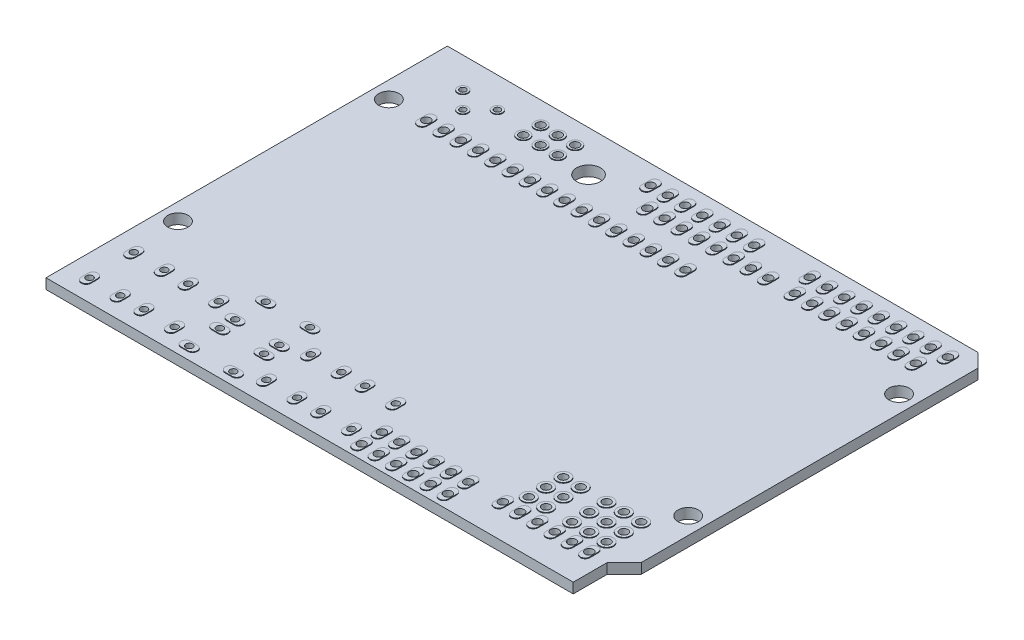
SolidWorks part; units mm, degrees
ref_plane "Front Plane" through (0, 0, 0) normal (0, 0, 1) x (1, 0, 0)
ref_plane "Top Plane" through (0, 0, 0) normal (0, 1, 0) x (1, 0, 0)
ref_plane "Right Plane" through (0, 0, 0) normal (1, 0, 0) x (0, 0, -1)
sketch "Sketch1" plane through (0, 0, 0) normal (0, 1, 0) x (1, 0, 0)
  line L0 (6.8, 54.47) -> (11.88, 54.47) construction
  line L1 (0, 0) -> (77.5, 0)
  line L2 (0, 0) -> (0, 59)
  line L3 (0, 59) -> (78, 59)
  line L4 (80, 7.5) -> (80, 57)
  line L5 (3.3, 9.6) -> (7.8, 9.6) construction
  line L6 (3.3, 9.6) -> (3.3, 3.1) construction
  line L7 (3.3, 3.1) -> (7.8, 3.1) construction
  line L8 (7.8, 9.6) -> (7.8, 3.1) construction
  line L9 (19.3, 6.25) -> (25.8, 6.25) construction
  line L10 (19.3, 6.25) -> (19.3, 1.75) construction
  line L11 (19.3, 1.75) -> (25.8, 1.75) construction
  line L12 (25.8, 6.25) -> (25.8, 1.75) construction
  line L13 (9.34, 54.47) -> (9.34, 51.93) construction
  line L14 (78, 59) -> (80, 57)
  line L15 (78, 59) -> (80, 59) construction
  line L16 (80, 59) -> (80, 57) construction
  line L17 (77.5, 0) -> (77.5, 5)
  line L18 (77.5, 5) -> (80, 7.5)
  line L19 (77.5, 0) -> (80, 0) construction
  line L20 (80, 0) -> (80, 7.5) construction
  line L21 (8, 47.9) -> (46.1, 47.9) construction
  circle A0 centre (17, 55.7) radius 0.6
  circle A1 centre (19.54, 55.7) radius 0.6
  circle A2 centre (22.08, 55.7) radius 0.6
  circle A3 centre (19.54, 53.16) radius 0.6
  circle A4 centre (22.08, 53.16) radius 0.6
  circle A5 centre (17, 53.16) radius 0.6
  circle A6 centre (32.7622, 56.1) radius 0.6
  circle A7 centre (35.4331, 52.95) radius 0.6
  circle A8 centre (35.3022, 56.1) radius 0.6
  circle A9 centre (37.8422, 56.1) radius 0.6
  circle A10 centre (40.3822, 56.1) radius 0.6
  circle A11 centre (42.9222, 56.1) radius 0.6
  circle A12 centre (45.4622, 56.1) radius 0.6
  circle A13 centre (48.0022, 56.1) radius 0.6
  circle A14 centre (37.9731, 52.95) radius 0.6
  circle A15 centre (40.5131, 52.95) radius 0.6
  circle A16 centre (43.0531, 52.95) radius 0.6
  circle A17 centre (45.5931, 52.95) radius 0.6
  circle A18 centre (48.1331, 52.95) radius 0.6
  circle A19 centre (50.6731, 52.95) radius 0.6
  circle A20 centre (53.2131, 52.95) radius 0.6
  circle A21 centre (56.1622, 56.1) radius 0.6
  circle A22 centre (57.1301, 52.95) radius 0.6
  circle A23 centre (59.6701, 52.95) radius 0.6
  circle A24 centre (62.2101, 52.95) radius 0.6
  circle A25 centre (64.7501, 52.95) radius 0.6
  circle A26 centre (67.2901, 52.95) radius 0.6
  circle A27 centre (69.8301, 52.95) radius 0.6
  circle A28 centre (72.3701, 52.95) radius 0.6
  circle A29 centre (74.9101, 52.95) radius 0.6
  circle A30 centre (58.7022, 56.1) radius 0.6
  circle A31 centre (61.2422, 56.1) radius 0.6
  circle A32 centre (63.7822, 56.1) radius 0.6
  circle A33 centre (66.3222, 56.1) radius 0.6
  circle A34 centre (68.8622, 56.1) radius 0.6
  circle A35 centre (71.4022, 56.1) radius 0.6
  circle A36 centre (73.9422, 56.1) radius 0.6
  circle A37 centre (76.4822, 56.1) radius 0.6
  circle A38 centre (8, 47.9) radius 0.6
  circle A39 centre (10.54, 47.9) radius 0.6
  circle A40 centre (13.08, 47.9) radius 0.6
  circle A41 centre (15.62, 47.9) radius 0.6
  circle A42 centre (18.16, 47.9) radius 0.6
  circle A43 centre (20.7, 47.9) radius 0.6
  circle A44 centre (23.24, 47.9) radius 0.6
  circle A45 centre (25.78, 47.9) radius 0.6
  circle A46 centre (28.32, 47.9) radius 0.6
  circle A47 centre (30.86, 47.9) radius 0.6
  circle A48 centre (33.4, 47.9) radius 0.6
  circle A49 centre (35.94, 47.9) radius 0.6
  circle A50 centre (38.48, 47.9) radius 0.6
  circle A51 centre (41.02, 47.9) radius 0.6
  circle A52 centre (43.56, 47.9) radius 0.6
  circle A53 centre (46.1, 47.9) radius 0.6
  circle A54 centre (74.9101, 4.95) radius 0.6
  circle A55 centre (72.3701, 4.95) radius 0.6
  circle A56 centre (69.8301, 4.95) radius 0.6
  circle A57 centre (67.2901, 4.95) radius 0.6
  circle A58 centre (64.7501, 4.95) radius 0.6
  circle A59 centre (62.2101, 4.95) radius 0.6
  circle A60 centre (59.6701, 4.95) radius 0.6 [skipped]
  circle A61 centre (57.1301, 4.95) radius 0.6
  circle A62 centre (54.5901, 4.95) radius 0.6
  circle A63 centre (52.0501, 4.95) radius 0.6
  circle A64 centre (49.5101, 4.95) radius 0.6
  circle A65 centre (46.9701, 4.95) radius 0.6
  circle A66 centre (44.4301, 4.95) radius 0.6
  circle A67 centre (57.1301, 1.95) radius 0.6
  circle A68 centre (54.5901, 1.95) radius 0.6
  circle A69 centre (52.0501, 1.95) radius 0.6
  circle A70 centre (49.5101, 1.95) radius 0.6
  circle A71 centre (46.9701, 1.95) radius 0.6
  circle A72 centre (44.4301, 1.95) radius 0.6
  circle A73 centre (63.4801, 7.49) radius 0.6
  circle A74 centre (74.9101, 7.49) radius 0.6
  circle A75 centre (72.3701, 7.49) radius 0.6
  circle A76 centre (69.8301, 7.49) radius 0.6
  circle A77 centre (74.9101, 10.03) radius 0.6
  circle A78 centre (72.3701, 10.03) radius 0.6
  circle A79 centre (69.8301, 10.03) radius 0.6
  circle A80 centre (74.9101, 12.57) radius 0.6
  circle A81 centre (72.3701, 12.57) radius 0.6
  circle A82 centre (69.8301, 12.57) radius 0.6
  circle A83 centre (66.0201, 7.49) radius 0.6
  circle A84 centre (66.0201, 10.03) radius 0.6
  circle A85 centre (66.0201, 12.57) radius 0.6
  circle A86 centre (63.4801, 10.03) radius 0.6
  circle A87 centre (63.4801, 12.57) radius 0.6
  circle A88 centre (2.5, 47.9) radius 1.5
  circle A89 centre (77.5, 47.9) radius 1.5
  circle A90 centre (77.5, 16.9) radius 1.5
  circle A91 centre (2.5, 16.9) radius 1.5
  circle A92 centre (3.3, 9.6) radius 0.5
  circle A93 centre (7.8, 9.6) radius 0.5
  circle A94 centre (7.8, 3.1) radius 0.5
  circle A95 centre (3.3, 3.1) radius 0.5
  circle A96 centre (11.3, 9.6) radius 0.5
  circle A97 centre (15.8, 9.6) radius 0.5
  circle A98 centre (15.8, 3.1) radius 0.5
  circle A99 centre (11.3, 3.1) radius 0.5
  circle A100 centre (29.3, 9.6) radius 0.5
  circle A101 centre (33.8, 9.6) radius 0.5
  circle A102 centre (33.8, 3.1) radius 0.5
  circle A103 centre (29.3, 3.1) radius 0.5
  circle A104 centre (41.8, 3.1) radius 0.5
  circle A105 centre (41.8, 9.6) radius 0.5
  circle A106 centre (37.3, 9.6) radius 0.5
  circle A107 centre (37.3, 3.1) radius 0.5
  circle A108 centre (19.3, 6.25) radius 0.5
  circle A109 centre (25.8, 6.25) radius 0.5
  circle A110 centre (25.8, 1.75) radius 0.5
  circle A111 centre (19.3, 1.75) radius 0.5
  circle A112 centre (19.3, 13) radius 0.5
  circle A113 centre (19.3, 8.5) radius 0.5
  circle A114 centre (25.8, 13) radius 0.5
  circle A115 centre (25.8, 8.5) radius 0.5
  circle A116 centre (6.8, 54.47) radius 0.45
  circle A117 centre (11.88, 54.47) radius 0.45
  circle A118 centre (9.34, 51.93) radius 0.45
  circle A119 centre (26.75, 53) radius 1.75
  point P1 (80, 59)
  point P3 (80, 0)
  point P243 (9.34, 54.47)
  dimension "D3" = 1.2
  dimension "D9" = 1.2
  dimension "D12" = 1.2
  dimension "D13" = 7
  dimension "D18" = 1.2
  dimension "D23" = 1.2
  dimension "D24" = 1.2
  dimension "D28" = 48
  dimension "D29" = 13
  dimension "D31" = 1.2
  dimension "D35" = 2
  dimension "D38" = 3
  dimension "D40" = 23.4
  dimension "D47" = 1
  dimension "D48" = 1
  dimension "D49" = 1
  dimension "D50" = 1
  dimension "D57" = 1
  dimension "D61" = 0.9
  dimension "D72" = 11.1
  dimension "D73" = 3.5
  dimension "D1" = 59
  dimension "D4" = 3.3
  dimension "D5" = 17
  dimension "D8" = 2.9
  dimension "D10" = 2
  dimension "D11" = 3.15
  dimension "D15" = 2.6709
  dimension "D16" = 2.9
  dimension "D17" = 3.15
  dimension "D19" = 3.917
  dimension "D21" = 15.7622
  dimension "D25" = 8
  dimension "D26" = 11.1
  dimension "D33" = 3.5
  dimension "D34" = 1.27
  dimension "D37" = 2.5
  dimension "D39" = 11.1
  dimension "D43" = 31
  dimension "D44" = 75
  dimension "D45" = 4.5
  dimension "D46" = 6.5
  dimension "D51" = 3.1
  dimension "D52" = 3.3
  dimension "D55" = 6.5
  dimension "D56" = 4.5
  dimension "D58" = 1.75
  dimension "D59" = 3.5
  dimension "D62" = 2.54
  dimension "D63" = 2.54
  dimension "D64" = 4.53
  dimension "D65" = 6.8
  dimension "D66" = 2
  dimension "D67" = 2
  dimension "D68" = 80
  dimension "D69" = 2.5
  dimension "D70" = 2.5
  dimension "D71" = 5
  dimension "D74" = 26.75
  dimension "D75" = 6
  dimension "D76" = 1.95
  dimension "D77" = 3
  dimension "D6" = 3
  dimension "D7" = 2
  dimension "D14" = 8
  dimension "D20" = 8
  dimension "D22" = 9
  dimension "D27" = 16
  dimension "D30" = 2
  dimension "D32" = 4
  dimension "D36" = 3
  dimension "D41" = 2
  dimension "D42" = 2
  dimension "D53" = 2
  dimension "D54" = 2
  dimension "D60" = 2
extrude "PCB" add sketch "Sketch1" against normal blind 1.5
sketch "Sketch2" plane through (0, 0, 0) normal (0, 1, 0) x (1, 0, 0)
  line L0 (32.7622, 56.7) -> (32.7622, 55.5) construction
  line L1 (32.7622, 56.7) -> (32.7622, 55.5) construction
  line L2 (33.4622, 56.7) -> (33.4622, 55.5)
  line L3 (32.0622, 56.7) -> (32.0622, 55.5)
  line L4 (35.3022, 56.7) -> (35.3022, 55.5) construction
  line L5 (35.3022, 56.7) -> (35.3022, 55.5) construction
  line L6 (36.0022, 56.7) -> (36.0022, 55.5)
  line L7 (34.6022, 56.7) -> (34.6022, 55.5)
  line L8 (37.8422, 56.7) -> (37.8422, 55.5) construction
  line L9 (37.8422, 56.7) -> (37.8422, 55.5) construction
  line L10 (38.5422, 56.7) -> (38.5422, 55.5)
  line L11 (37.1422, 56.7) -> (37.1422, 55.5)
  line L12 (40.3822, 56.7) -> (40.3822, 55.5) construction
  line L13 (40.3822, 56.7) -> (40.3822, 55.5) construction
  line L14 (41.0822, 56.7) -> (41.0822, 55.5)
  line L15 (39.6822, 56.7) -> (39.6822, 55.5)
  line L16 (42.9222, 56.7) -> (42.9222, 55.5) construction
  line L17 (42.9222, 56.7) -> (42.9222, 55.5) construction
  line L18 (43.6222, 56.7) -> (43.6222, 55.5)
  line L19 (42.2222, 56.7) -> (42.2222, 55.5)
  line L20 (45.4622, 56.7) -> (45.4622, 55.5) construction
  line L21 (45.4622, 56.7) -> (45.4622, 55.5) construction
  line L22 (46.1622, 56.7) -> (46.1622, 55.5)
  line L23 (44.7622, 56.7) -> (44.7622, 55.5)
  line L24 (48.0022, 56.7) -> (48.0022, 55.5) construction
  line L25 (48.0022, 56.7) -> (48.0022, 55.5) construction
  line L26 (48.7022, 56.7) -> (48.7022, 55.5)
  line L27 (47.3022, 56.7) -> (47.3022, 55.5)
  line L28 (35.4331, 53.55) -> (35.4331, 52.35) construction
  line L29 (36.1331, 53.55) -> (36.1331, 52.35)
  line L30 (34.7331, 53.55) -> (34.7331, 52.35)
  line L31 (56.1622, 56.7) -> (56.1622, 55.5) construction
  line L32 (56.8622, 56.7) -> (56.8622, 55.5)
  line L33 (55.4622, 56.7) -> (55.4622, 55.5)
  line L34 (57.1301, 53.55) -> (57.1301, 52.35) construction
  line L35 (57.8301, 53.55) -> (57.8301, 52.35)
  line L36 (56.4301, 53.55) -> (56.4301, 52.35)
  line L37 (8, 48.5) -> (8, 47.3) construction
  line L38 (8.7, 48.5) -> (8.7, 47.3)
  line L39 (7.3, 48.5) -> (7.3, 47.3)
  line L40 (3.3, 10.1) -> (3.3, 9.1) construction
  line L41 (4, 10.1) -> (4, 9.1)
  line L42 (2.6, 10.1) -> (2.6, 9.1)
  line L43 (18.8, 1.75) -> (19.8, 1.75) construction
  line L44 (18.8, 2.45) -> (19.8, 2.45)
  line L45 (18.8, 1.05) -> (19.8, 1.05)
  line L46 (29.3, 10.1) -> (29.3, 9.1) construction
  line L47 (30, 10.1) -> (30, 9.1)
  line L48 (28.6, 10.1) -> (28.6, 9.1)
  line L49 (44.4301, 5.55) -> (44.4301, 4.35) construction
  line L50 (45.1301, 5.55) -> (45.1301, 4.35)
  line L51 (43.7301, 5.55) -> (43.7301, 4.35)
  line L52 (62.2101, 4.35) -> (62.2101, 5.55) construction
  line L53 (61.5101, 4.35) -> (61.5101, 5.55)
  line L54 (62.9101, 4.35) -> (62.9101, 5.55)
  line L55 (7.8, 10.1) -> (7.8, 9.1) construction
  line L56 (8.5, 10.1) -> (8.5, 9.1)
  line L57 (7.1, 10.1) -> (7.1, 9.1)
  line L58 (7.8, 3.6) -> (7.8, 2.6) construction
  line L59 (8.5, 3.6) -> (8.5, 2.6)
  line L60 (7.1, 3.6) -> (7.1, 2.6)
  line L61 (37.9731, 53.55) -> (37.9731, 52.35) construction
  line L62 (38.6731, 53.55) -> (38.6731, 52.35)
  line L63 (37.2731, 53.55) -> (37.2731, 52.35)
  line L64 (59.6701, 53.55) -> (59.6701, 52.35) construction
  line L65 (60.3701, 53.55) -> (60.3701, 52.35)
  line L66 (58.9701, 53.55) -> (58.9701, 52.35)
  line L67 (40.5131, 53.55) -> (40.5131, 52.35) construction
  line L68 (41.2131, 53.55) -> (41.2131, 52.35)
  line L69 (39.8131, 53.55) -> (39.8131, 52.35)
  line L70 (62.2101, 53.55) -> (62.2101, 52.35) construction
  line L71 (62.9101, 53.55) -> (62.9101, 52.35)
  line L72 (61.5101, 53.55) -> (61.5101, 52.35)
  line L73 (43.0531, 53.55) -> (43.0531, 52.35) construction
  line L74 (43.7531, 53.55) -> (43.7531, 52.35)
  line L75 (42.3531, 53.55) -> (42.3531, 52.35)
  line L76 (64.7501, 53.55) -> (64.7501, 52.35) construction
  line L77 (65.4501, 53.55) -> (65.4501, 52.35)
  line L78 (64.0501, 53.55) -> (64.0501, 52.35)
  line L79 (45.5931, 53.55) -> (45.5931, 52.35) construction
  line L80 (46.2931, 53.55) -> (46.2931, 52.35)
  line L81 (44.8931, 53.55) -> (44.8931, 52.35)
  line L82 (67.2901, 53.55) -> (67.2901, 52.35) construction
  line L83 (67.9901, 53.55) -> (67.9901, 52.35)
  line L84 (66.5901, 53.55) -> (66.5901, 52.35)
  line L85 (48.1331, 53.55) -> (48.1331, 52.35) construction
  line L86 (48.8331, 53.55) -> (48.8331, 52.35)
  line L87 (47.4331, 53.55) -> (47.4331, 52.35)
  line L88 (69.8301, 53.55) -> (69.8301, 52.35) construction
  line L89 (70.5301, 53.55) -> (70.5301, 52.35)
  line L90 (69.1301, 53.55) -> (69.1301, 52.35)
  line L91 (50.6731, 53.55) -> (50.6731, 52.35) construction
  line L92 (51.3731, 53.55) -> (51.3731, 52.35)
  line L93 (49.9731, 53.55) -> (49.9731, 52.35)
  line L94 (72.3701, 53.55) -> (72.3701, 52.35) construction
  line L95 (73.0701, 53.55) -> (73.0701, 52.35)
  line L96 (71.6701, 53.55) -> (71.6701, 52.35)
  line L97 (53.2131, 53.55) -> (53.2131, 52.35) construction
  line L98 (53.9131, 53.55) -> (53.9131, 52.35)
  line L99 (52.5131, 53.55) -> (52.5131, 52.35)
  line L100 (74.9101, 53.55) -> (74.9101, 52.35) construction
  line L101 (75.6101, 53.55) -> (75.6101, 52.35)
  line L102 (74.2101, 53.55) -> (74.2101, 52.35)
  line L103 (58.7022, 56.7) -> (58.7022, 55.5) construction
  line L104 (59.4022, 56.7) -> (59.4022, 55.5)
  line L105 (58.0022, 56.7) -> (58.0022, 55.5)
  line L106 (61.2422, 56.7) -> (61.2422, 55.5) construction
  line L107 (61.9422, 56.7) -> (61.9422, 55.5)
  line L108 (60.5422, 56.7) -> (60.5422, 55.5)
  line L109 (63.7822, 56.7) -> (63.7822, 55.5) construction
  line L110 (64.4822, 56.7) -> (64.4822, 55.5)
  line L111 (63.0822, 56.7) -> (63.0822, 55.5)
  line L112 (66.3222, 56.7) -> (66.3222, 55.5) construction
  line L113 (67.0222, 56.7) -> (67.0222, 55.5)
  line L114 (65.6222, 56.7) -> (65.6222, 55.5)
  line L115 (68.8622, 56.7) -> (68.8622, 55.5) construction
  line L116 (69.5622, 56.7) -> (69.5622, 55.5)
  line L117 (68.1622, 56.7) -> (68.1622, 55.5)
  line L118 (71.4022, 56.7) -> (71.4022, 55.5) construction
  line L119 (72.1022, 56.7) -> (72.1022, 55.5)
  line L120 (70.7022, 56.7) -> (70.7022, 55.5)
  line L121 (73.9422, 56.7) -> (73.9422, 55.5) construction
  line L122 (74.6422, 56.7) -> (74.6422, 55.5)
  line L123 (73.2422, 56.7) -> (73.2422, 55.5)
  line L124 (76.4822, 56.7) -> (76.4822, 55.5) construction
  line L125 (77.1822, 56.7) -> (77.1822, 55.5)
  line L126 (75.7822, 56.7) -> (75.7822, 55.5)
  line L127 (10.54, 48.5) -> (10.54, 47.3) construction
  line L128 (11.24, 48.5) -> (11.24, 47.3)
  line L129 (9.84, 48.5) -> (9.84, 47.3)
  line L130 (13.08, 48.5) -> (13.08, 47.3) construction
  line L131 (13.78, 48.5) -> (13.78, 47.3)
  line L132 (12.38, 48.5) -> (12.38, 47.3)
  line L133 (15.62, 48.5) -> (15.62, 47.3) construction
  line L134 (16.32, 48.5) -> (16.32, 47.3)
  line L135 (14.92, 48.5) -> (14.92, 47.3)
  line L136 (18.16, 48.5) -> (18.16, 47.3) construction
  line L137 (18.86, 48.5) -> (18.86, 47.3)
  line L138 (17.46, 48.5) -> (17.46, 47.3)
  line L139 (20.7, 48.5) -> (20.7, 47.3) construction
  line L140 (21.4, 48.5) -> (21.4, 47.3)
  line L141 (20, 48.5) -> (20, 47.3)
  line L142 (23.24, 48.5) -> (23.24, 47.3) construction
  line L143 (23.94, 48.5) -> (23.94, 47.3)
  line L144 (22.54, 48.5) -> (22.54, 47.3)
  line L145 (25.78, 48.5) -> (25.78, 47.3) construction
  line L146 (26.48, 48.5) -> (26.48, 47.3)
  line L147 (25.08, 48.5) -> (25.08, 47.3)
  line L148 (28.32, 48.5) -> (28.32, 47.3) construction
  line L149 (29.02, 48.5) -> (29.02, 47.3)
  line L150 (27.62, 48.5) -> (27.62, 47.3)
  line L151 (30.86, 48.5) -> (30.86, 47.3) construction
  line L152 (31.56, 48.5) -> (31.56, 47.3)
  line L153 (30.16, 48.5) -> (30.16, 47.3)
  line L154 (33.4, 48.5) -> (33.4, 47.3) construction
  line L155 (34.1, 48.5) -> (34.1, 47.3)
  line L156 (32.7, 48.5) -> (32.7, 47.3)
  line L157 (35.94, 48.5) -> (35.94, 47.3) construction
  line L158 (36.64, 48.5) -> (36.64, 47.3)
  line L159 (35.24, 48.5) -> (35.24, 47.3)
  line L160 (38.48, 48.5) -> (38.48, 47.3) construction
  line L161 (39.18, 48.5) -> (39.18, 47.3)
  line L162 (37.78, 48.5) -> (37.78, 47.3)
  line L163 (41.02, 48.5) -> (41.02, 47.3) construction
  line L164 (41.72, 48.5) -> (41.72, 47.3)
  line L165 (40.32, 48.5) -> (40.32, 47.3)
  line L166 (43.56, 48.5) -> (43.56, 47.3) construction
  line L167 (44.26, 48.5) -> (44.26, 47.3)
  line L168 (42.86, 48.5) -> (42.86, 47.3)
  line L169 (46.1, 48.5) -> (46.1, 47.3) construction
  line L170 (46.8, 48.5) -> (46.8, 47.3)
  line L171 (45.4, 48.5) -> (45.4, 47.3)
  line L172 (46.9701, 5.55) -> (46.9701, 4.35) construction
  line L173 (47.6701, 5.55) -> (47.6701, 4.35)
  line L174 (46.2701, 5.55) -> (46.2701, 4.35)
  line L175 (49.5101, 5.55) -> (49.5101, 4.35) construction
  line L176 (50.2101, 5.55) -> (50.2101, 4.35)
  line L177 (48.8101, 5.55) -> (48.8101, 4.35)
  line L178 (52.0501, 5.55) -> (52.0501, 4.35) construction
  line L179 (52.7501, 5.55) -> (52.7501, 4.35)
  line L180 (51.3501, 5.55) -> (51.3501, 4.35)
  line L181 (54.5901, 5.55) -> (54.5901, 4.35) construction
  line L182 (55.2901, 5.55) -> (55.2901, 4.35)
  line L183 (53.8901, 5.55) -> (53.8901, 4.35)
  line L184 (57.1301, 5.55) -> (57.1301, 4.35) construction
  line L185 (57.8301, 5.55) -> (57.8301, 4.35)
  line L186 (56.4301, 5.55) -> (56.4301, 4.35)
  line L187 (46.9701, 2.55) -> (46.9701, 1.35) construction
  line L188 (47.6701, 2.55) -> (47.6701, 1.35)
  line L189 (46.2701, 2.55) -> (46.2701, 1.35)
  line L190 (49.5101, 2.55) -> (49.5101, 1.35) construction
  line L191 (50.2101, 2.55) -> (50.2101, 1.35)
  line L192 (48.8101, 2.55) -> (48.8101, 1.35)
  line L193 (52.0501, 2.55) -> (52.0501, 1.35) construction
  line L194 (52.7501, 2.55) -> (52.7501, 1.35)
  line L195 (51.3501, 2.55) -> (51.3501, 1.35)
  line L196 (54.5901, 2.55) -> (54.5901, 1.35) construction
  line L197 (55.2901, 2.55) -> (55.2901, 1.35)
  line L198 (53.8901, 2.55) -> (53.8901, 1.35)
  line L199 (57.1301, 2.55) -> (57.1301, 1.35) construction
  line L200 (57.8301, 2.55) -> (57.8301, 1.35)
  line L201 (56.4301, 2.55) -> (56.4301, 1.35)
  line L202 (44.4301, 2.55) -> (44.4301, 1.35) construction
  line L203 (45.1301, 2.55) -> (45.1301, 1.35)
  line L204 (43.7301, 2.55) -> (43.7301, 1.35)
  line L205 (64.7501, 4.35) -> (64.7501, 5.55) construction
  line L206 (64.0501, 4.35) -> (64.0501, 5.55)
  line L207 (65.4501, 4.35) -> (65.4501, 5.55)
  line L208 (67.2901, 4.35) -> (67.2901, 5.55) construction
  line L209 (66.5901, 4.35) -> (66.5901, 5.55)
  line L210 (67.9901, 4.35) -> (67.9901, 5.55)
  line L211 (69.8301, 4.35) -> (69.8301, 5.55) construction
  line L212 (69.1301, 4.35) -> (69.1301, 5.55)
  line L213 (70.5301, 4.35) -> (70.5301, 5.55)
  line L214 (72.3701, 4.35) -> (72.3701, 5.55) construction
  line L215 (71.6701, 4.35) -> (71.6701, 5.55)
  line L216 (73.0701, 4.35) -> (73.0701, 5.55)
  line L217 (74.9101, 4.35) -> (74.9101, 5.55) construction
  line L218 (74.2101, 4.35) -> (74.2101, 5.55)
  line L219 (75.6101, 4.35) -> (75.6101, 5.55)
  line L220 (3.3, 3.6) -> (3.3, 2.6) construction
  line L221 (4, 3.6) -> (4, 2.6)
  line L222 (2.6, 3.6) -> (2.6, 2.6)
  line L223 (11.3, 10.1) -> (11.3, 9.1) construction
  line L224 (12, 10.1) -> (12, 9.1)
  line L225 (10.6, 10.1) -> (10.6, 9.1)
  line L226 (15.8, 10.1) -> (15.8, 9.1) construction
  line L227 (16.5, 10.1) -> (16.5, 9.1)
  line L228 (15.1, 10.1) -> (15.1, 9.1)
  line L229 (15.8, 3.6) -> (15.8, 2.6) construction
  line L230 (16.5, 3.6) -> (16.5, 2.6)
  line L231 (15.1, 3.6) -> (15.1, 2.6)
  line L232 (11.3, 3.6) -> (11.3, 2.6) construction
  line L233 (12, 3.6) -> (12, 2.6)
  line L234 (10.6, 3.6) -> (10.6, 2.6)
  line L235 (25.3, 1.75) -> (26.3, 1.75) construction
  line L236 (25.3, 2.45) -> (26.3, 2.45)
  line L237 (25.3, 1.05) -> (26.3, 1.05)
  line L238 (25.3, 6.25) -> (26.3, 6.25) construction
  line L239 (25.3, 6.95) -> (26.3, 6.95)
  line L240 (25.3, 5.55) -> (26.3, 5.55)
  line L241 (18.8, 6.25) -> (19.8, 6.25) construction
  line L242 (18.8, 6.95) -> (19.8, 6.95)
  line L243 (18.8, 5.55) -> (19.8, 5.55)
  line L244 (18.8, 8.5) -> (19.8, 8.5) construction
  line L245 (18.8, 9.2) -> (19.8, 9.2)
  line L246 (18.8, 7.8) -> (19.8, 7.8)
  line L247 (25.3, 8.5) -> (26.3, 8.5) construction
  line L248 (25.3, 9.2) -> (26.3, 9.2)
  line L249 (25.3, 7.8) -> (26.3, 7.8)
  line L250 (25.3, 13) -> (26.3, 13) construction
  line L251 (25.3, 13.7) -> (26.3, 13.7)
  line L252 (25.3, 12.3) -> (26.3, 12.3)
  line L253 (18.8, 13) -> (19.8, 13) construction
  line L254 (18.8, 13.7) -> (19.8, 13.7)
  line L255 (18.8, 12.3) -> (19.8, 12.3)
  line L256 (33.8, 10.1) -> (33.8, 9.1) construction
  line L257 (34.5, 10.1) -> (34.5, 9.1)
  line L258 (33.1, 10.1) -> (33.1, 9.1)
  line L259 (33.8, 3.6) -> (33.8, 2.6) construction
  line L260 (34.5, 3.6) -> (34.5, 2.6)
  line L261 (33.1, 3.6) -> (33.1, 2.6)
  line L262 (29.3, 3.6) -> (29.3, 2.6) construction
  line L263 (30, 3.6) -> (30, 2.6)
  line L264 (28.6, 3.6) -> (28.6, 2.6)
  line L265 (37.3, 10.1) -> (37.3, 9.1) construction
  line L266 (38, 10.1) -> (38, 9.1)
  line L267 (36.6, 10.1) -> (36.6, 9.1)
  line L268 (41.8, 10.1) -> (41.8, 9.1) construction
  line L269 (42.5, 10.1) -> (42.5, 9.1)
  line L270 (41.1, 10.1) -> (41.1, 9.1)
  line L271 (41.8, 3.6) -> (41.8, 2.6) construction
  line L272 (42.5, 3.6) -> (42.5, 2.6)
  line L273 (41.1, 3.6) -> (41.1, 2.6)
  line L274 (37.3, 3.6) -> (37.3, 2.6) construction
  line L275 (38, 3.6) -> (38, 2.6)
  line L276 (36.6, 3.6) -> (36.6, 2.6)
  circle A0 centre (17, 55.7) radius 0.6 construction
  circle A1 centre (17, 53.16) radius 0.6 construction
  circle A2 centre (19.54, 53.16) radius 0.6 construction
  circle A3 centre (19.54, 55.7) radius 0.6 construction
  circle A4 centre (22.08, 55.7) radius 0.6 construction
  circle A5 centre (22.08, 53.16) radius 0.6 construction
  circle A6 centre (17, 55.7) radius 0.6
  circle A7 centre (17, 53.16) radius 0.6
  circle A8 centre (19.54, 53.16) radius 0.6
  circle A9 centre (19.54, 55.7) radius 0.6
  circle A10 centre (22.08, 55.7) radius 0.6
  circle A11 centre (22.08, 53.16) radius 0.6
  circle A12 centre (17, 55.7) radius 0.9
  circle A13 centre (17, 53.16) radius 0.9
  circle A14 centre (19.54, 53.16) radius 0.9
  circle A15 centre (19.54, 55.7) radius 0.9
  circle A16 centre (22.08, 55.7) radius 0.9
  circle A17 centre (22.08, 53.16) radius 0.9
  circle A18 centre (32.7622, 56.1) radius 0.6 construction
  circle A19 centre (32.7622, 56.1) radius 0.6
  arc A20 (33.4622, 56.7) -> (32.0622, 56.7) centre (32.7622, 56.7) ccw
  arc A21 (32.0622, 55.5) -> (33.4622, 55.5) centre (32.7622, 55.5) ccw
  circle A22 centre (35.3022, 56.1) radius 0.6
  arc A23 (36.0022, 56.7) -> (34.6022, 56.7) centre (35.3022, 56.7) ccw
  arc A24 (34.6022, 55.5) -> (36.0022, 55.5) centre (35.3022, 55.5) ccw
  circle A25 centre (37.8422, 56.1) radius 0.6
  arc A26 (38.5422, 56.7) -> (37.1422, 56.7) centre (37.8422, 56.7) ccw
  arc A27 (37.1422, 55.5) -> (38.5422, 55.5) centre (37.8422, 55.5) ccw
  circle A28 centre (40.3822, 56.1) radius 0.6
  arc A29 (41.0822, 56.7) -> (39.6822, 56.7) centre (40.3822, 56.7) ccw
  arc A30 (39.6822, 55.5) -> (41.0822, 55.5) centre (40.3822, 55.5) ccw
  circle A31 centre (42.9222, 56.1) radius 0.6
  arc A32 (43.6222, 56.7) -> (42.2222, 56.7) centre (42.9222, 56.7) ccw
  arc A33 (42.2222, 55.5) -> (43.6222, 55.5) centre (42.9222, 55.5) ccw
  circle A34 centre (45.4622, 56.1) radius 0.6
  arc A35 (46.1622, 56.7) -> (44.7622, 56.7) centre (45.4622, 56.7) ccw
  arc A36 (44.7622, 55.5) -> (46.1622, 55.5) centre (45.4622, 55.5) ccw
  circle A37 centre (48.0022, 56.1) radius 0.6
  arc A38 (48.7022, 56.7) -> (47.3022, 56.7) centre (48.0022, 56.7) ccw
  arc A39 (47.3022, 55.5) -> (48.7022, 55.5) centre (48.0022, 55.5) ccw
  circle A40 centre (35.4331, 52.95) radius 0.6 construction
  circle A41 centre (56.1622, 56.1) radius 0.6 construction
  circle A42 centre (57.1301, 52.95) radius 0.6 construction
  circle A43 centre (8, 47.9) radius 0.6 construction
  circle A44 centre (35.4331, 52.95) radius 0.6
  circle A45 centre (56.1622, 56.1) radius 0.6
  circle A46 centre (57.1301, 52.95) radius 0.6
  circle A47 centre (8, 47.9) radius 0.6
  arc A48 (36.1331, 53.55) -> (34.7331, 53.55) centre (35.4331, 53.55) ccw
  arc A49 (34.7331, 52.35) -> (36.1331, 52.35) centre (35.4331, 52.35) ccw
  arc A50 (56.8622, 56.7) -> (55.4622, 56.7) centre (56.1622, 56.7) ccw
  arc A51 (55.4622, 55.5) -> (56.8622, 55.5) centre (56.1622, 55.5) ccw
  arc A52 (57.8301, 53.55) -> (56.4301, 53.55) centre (57.1301, 53.55) ccw
  arc A53 (56.4301, 52.35) -> (57.8301, 52.35) centre (57.1301, 52.35) ccw
  arc A54 (8.7, 48.5) -> (7.3, 48.5) centre (8, 48.5) ccw
  arc A55 (7.3, 47.3) -> (8.7, 47.3) centre (8, 47.3) ccw
  circle A56 centre (37.9731, 52.95) radius 0.6
  circle A57 centre (19.3, 1.75) radius 0.5 construction
  circle A58 centre (29.3, 9.6) radius 0.5 construction
  circle A59 centre (44.4301, 4.95) radius 0.6 construction
  circle A60 centre (62.2101, 4.95) radius 0.6 construction
  circle A61 centre (63.4801, 7.49) radius 0.6 construction
  circle A62 centre (69.8301, 7.49) radius 0.6 construction
  circle A63 centre (3.3, 9.6) radius 0.5 construction
  circle A64 centre (19.3, 1.75) radius 0.5
  circle A65 centre (29.3, 9.6) radius 0.5
  circle A66 centre (44.4301, 4.95) radius 0.6
  circle A67 centre (62.2101, 4.95) radius 0.6
  circle A68 centre (63.4801, 7.49) radius 0.6
  circle A69 centre (69.8301, 7.49) radius 0.6
  circle A70 centre (3.3, 9.6) radius 0.5
  arc A71 (4, 10.1) -> (2.6, 10.1) centre (3.3, 10.1) ccw
  arc A72 (18.8, 2.45) -> (18.8, 1.05) centre (18.8, 1.75) ccw
  arc A73 (19.8, 1.05) -> (19.8, 2.45) centre (19.8, 1.75) ccw
  arc A74 (30, 10.1) -> (28.6, 10.1) centre (29.3, 10.1) ccw
  arc A75 (28.6, 9.1) -> (30, 9.1) centre (29.3, 9.1) ccw
  arc A76 (45.1301, 5.55) -> (43.7301, 5.55) centre (44.4301, 5.55) ccw
  arc A77 (43.7301, 4.35) -> (45.1301, 4.35) centre (44.4301, 4.35) ccw
  arc A78 (61.5101, 4.35) -> (62.9101, 4.35) centre (62.2101, 4.35) ccw
  arc A79 (62.9101, 5.55) -> (61.5101, 5.55) centre (62.2101, 5.55) ccw
  circle A80 centre (63.4801, 12.57) radius 0.6 construction
  circle A81 centre (63.4801, 10.03) radius 0.6 construction
  circle A82 centre (66.0201, 7.49) radius 0.6 construction
  circle A83 centre (66.0201, 10.03) radius 0.6 construction
  arc A84 (2.6, 9.1) -> (4, 9.1) centre (3.3, 9.1) ccw
  circle A85 centre (59.6701, 52.95) radius 0.6
  arc A86 (38.6731, 53.55) -> (37.2731, 53.55) centre (37.9731, 53.55) ccw
  arc A87 (37.2731, 52.35) -> (38.6731, 52.35) centre (37.9731, 52.35) ccw
  arc A88 (60.3701, 53.55) -> (58.9701, 53.55) centre (59.6701, 53.55) ccw
  arc A89 (58.9701, 52.35) -> (60.3701, 52.35) centre (59.6701, 52.35) ccw
  circle A90 centre (40.5131, 52.95) radius 0.6
  circle A91 centre (62.2101, 52.95) radius 0.6
  arc A92 (41.2131, 53.55) -> (39.8131, 53.55) centre (40.5131, 53.55) ccw
  arc A93 (39.8131, 52.35) -> (41.2131, 52.35) centre (40.5131, 52.35) ccw
  arc A94 (62.9101, 53.55) -> (61.5101, 53.55) centre (62.2101, 53.55) ccw
  arc A95 (61.5101, 52.35) -> (62.9101, 52.35) centre (62.2101, 52.35) ccw
  circle A96 centre (43.0531, 52.95) radius 0.6
  circle A97 centre (64.7501, 52.95) radius 0.6
  arc A98 (43.7531, 53.55) -> (42.3531, 53.55) centre (43.0531, 53.55) ccw
  arc A99 (42.3531, 52.35) -> (43.7531, 52.35) centre (43.0531, 52.35) ccw
  arc A100 (65.4501, 53.55) -> (64.0501, 53.55) centre (64.7501, 53.55) ccw
  arc A101 (64.0501, 52.35) -> (65.4501, 52.35) centre (64.7501, 52.35) ccw
  circle A102 centre (45.5931, 52.95) radius 0.6
  circle A103 centre (67.2901, 52.95) radius 0.6
  arc A104 (46.2931, 53.55) -> (44.8931, 53.55) centre (45.5931, 53.55) ccw
  arc A105 (44.8931, 52.35) -> (46.2931, 52.35) centre (45.5931, 52.35) ccw
  arc A106 (67.9901, 53.55) -> (66.5901, 53.55) centre (67.2901, 53.55) ccw
  arc A107 (66.5901, 52.35) -> (67.9901, 52.35) centre (67.2901, 52.35) ccw
  circle A108 centre (48.1331, 52.95) radius 0.6
  circle A109 centre (69.8301, 52.95) radius 0.6
  arc A110 (48.8331, 53.55) -> (47.4331, 53.55) centre (48.1331, 53.55) ccw
  arc A111 (47.4331, 52.35) -> (48.8331, 52.35) centre (48.1331, 52.35) ccw
  arc A112 (70.5301, 53.55) -> (69.1301, 53.55) centre (69.8301, 53.55) ccw
  arc A113 (69.1301, 52.35) -> (70.5301, 52.35) centre (69.8301, 52.35) ccw
  circle A114 centre (50.6731, 52.95) radius 0.6
  circle A115 centre (72.3701, 52.95) radius 0.6
  arc A116 (51.3731, 53.55) -> (49.9731, 53.55) centre (50.6731, 53.55) ccw
  arc A117 (49.9731, 52.35) -> (51.3731, 52.35) centre (50.6731, 52.35) ccw
  arc A118 (73.0701, 53.55) -> (71.6701, 53.55) centre (72.3701, 53.55) ccw
  arc A119 (71.6701, 52.35) -> (73.0701, 52.35) centre (72.3701, 52.35) ccw
  circle A120 centre (53.2131, 52.95) radius 0.6
  circle A121 centre (74.9101, 52.95) radius 0.6
  arc A122 (53.9131, 53.55) -> (52.5131, 53.55) centre (53.2131, 53.55) ccw
  arc A123 (52.5131, 52.35) -> (53.9131, 52.35) centre (53.2131, 52.35) ccw
  arc A124 (75.6101, 53.55) -> (74.2101, 53.55) centre (74.9101, 53.55) ccw
  arc A125 (74.2101, 52.35) -> (75.6101, 52.35) centre (74.9101, 52.35) ccw
  circle A126 centre (58.7022, 56.1) radius 0.6
  arc A127 (59.4022, 56.7) -> (58.0022, 56.7) centre (58.7022, 56.7) ccw
  arc A128 (58.0022, 55.5) -> (59.4022, 55.5) centre (58.7022, 55.5) ccw
  circle A129 centre (61.2422, 56.1) radius 0.6
  arc A130 (61.9422, 56.7) -> (60.5422, 56.7) centre (61.2422, 56.7) ccw
  arc A131 (60.5422, 55.5) -> (61.9422, 55.5) centre (61.2422, 55.5) ccw
  circle A132 centre (63.7822, 56.1) radius 0.6
  arc A133 (64.4822, 56.7) -> (63.0822, 56.7) centre (63.7822, 56.7) ccw
  arc A134 (63.0822, 55.5) -> (64.4822, 55.5) centre (63.7822, 55.5) ccw
  circle A135 centre (66.3222, 56.1) radius 0.6
  arc A136 (67.0222, 56.7) -> (65.6222, 56.7) centre (66.3222, 56.7) ccw
  arc A137 (65.6222, 55.5) -> (67.0222, 55.5) centre (66.3222, 55.5) ccw
  circle A138 centre (68.8622, 56.1) radius 0.6
  arc A139 (69.5622, 56.7) -> (68.1622, 56.7) centre (68.8622, 56.7) ccw
  arc A140 (68.1622, 55.5) -> (69.5622, 55.5) centre (68.8622, 55.5) ccw
  circle A141 centre (71.4022, 56.1) radius 0.6
  arc A142 (72.1022, 56.7) -> (70.7022, 56.7) centre (71.4022, 56.7) ccw
  arc A143 (70.7022, 55.5) -> (72.1022, 55.5) centre (71.4022, 55.5) ccw
  circle A144 centre (73.9422, 56.1) radius 0.6
  arc A145 (74.6422, 56.7) -> (73.2422, 56.7) centre (73.9422, 56.7) ccw
  arc A146 (73.2422, 55.5) -> (74.6422, 55.5) centre (73.9422, 55.5) ccw
  circle A147 centre (76.4822, 56.1) radius 0.6
  arc A148 (77.1822, 56.7) -> (75.7822, 56.7) centre (76.4822, 56.7) ccw
  arc A149 (75.7822, 55.5) -> (77.1822, 55.5) centre (76.4822, 55.5) ccw
  circle A150 centre (10.54, 47.9) radius 0.6
  arc A151 (11.24, 48.5) -> (9.84, 48.5) centre (10.54, 48.5) ccw
  arc A152 (9.84, 47.3) -> (11.24, 47.3) centre (10.54, 47.3) ccw
  circle A153 centre (13.08, 47.9) radius 0.6
  arc A154 (13.78, 48.5) -> (12.38, 48.5) centre (13.08, 48.5) ccw
  arc A155 (12.38, 47.3) -> (13.78, 47.3) centre (13.08, 47.3) ccw
  circle A156 centre (15.62, 47.9) radius 0.6
  arc A157 (16.32, 48.5) -> (14.92, 48.5) centre (15.62, 48.5) ccw
  arc A158 (14.92, 47.3) -> (16.32, 47.3) centre (15.62, 47.3) ccw
  circle A159 centre (18.16, 47.9) radius 0.6
  arc A160 (18.86, 48.5) -> (17.46, 48.5) centre (18.16, 48.5) ccw
  arc A161 (17.46, 47.3) -> (18.86, 47.3) centre (18.16, 47.3) ccw
  circle A162 centre (20.7, 47.9) radius 0.6
  arc A163 (21.4, 48.5) -> (20, 48.5) centre (20.7, 48.5) ccw
  arc A164 (20, 47.3) -> (21.4, 47.3) centre (20.7, 47.3) ccw
  circle A165 centre (23.24, 47.9) radius 0.6
  arc A166 (23.94, 48.5) -> (22.54, 48.5) centre (23.24, 48.5) ccw
  arc A167 (22.54, 47.3) -> (23.94, 47.3) centre (23.24, 47.3) ccw
  circle A168 centre (25.78, 47.9) radius 0.6
  arc A169 (26.48, 48.5) -> (25.08, 48.5) centre (25.78, 48.5) ccw
  arc A170 (25.08, 47.3) -> (26.48, 47.3) centre (25.78, 47.3) ccw
  circle A171 centre (28.32, 47.9) radius 0.6
  arc A172 (29.02, 48.5) -> (27.62, 48.5) centre (28.32, 48.5) ccw
  arc A173 (27.62, 47.3) -> (29.02, 47.3) centre (28.32, 47.3) ccw
  circle A174 centre (30.86, 47.9) radius 0.6
  arc A175 (31.56, 48.5) -> (30.16, 48.5) centre (30.86, 48.5) ccw
  arc A176 (30.16, 47.3) -> (31.56, 47.3) centre (30.86, 47.3) ccw
  circle A177 centre (33.4, 47.9) radius 0.6
  arc A178 (34.1, 48.5) -> (32.7, 48.5) centre (33.4, 48.5) ccw
  arc A179 (32.7, 47.3) -> (34.1, 47.3) centre (33.4, 47.3) ccw
  circle A180 centre (35.94, 47.9) radius 0.6
  arc A181 (36.64, 48.5) -> (35.24, 48.5) centre (35.94, 48.5) ccw
  arc A182 (35.24, 47.3) -> (36.64, 47.3) centre (35.94, 47.3) ccw
  circle A183 centre (38.48, 47.9) radius 0.6
  arc A184 (39.18, 48.5) -> (37.78, 48.5) centre (38.48, 48.5) ccw
  arc A185 (37.78, 47.3) -> (39.18, 47.3) centre (38.48, 47.3) ccw
  circle A186 centre (41.02, 47.9) radius 0.6
  arc A187 (41.72, 48.5) -> (40.32, 48.5) centre (41.02, 48.5) ccw
  arc A188 (40.32, 47.3) -> (41.72, 47.3) centre (41.02, 47.3) ccw
  circle A189 centre (43.56, 47.9) radius 0.6
  arc A190 (44.26, 48.5) -> (42.86, 48.5) centre (43.56, 48.5) ccw
  arc A191 (42.86, 47.3) -> (44.26, 47.3) centre (43.56, 47.3) ccw
  circle A192 centre (46.1, 47.9) radius 0.6
  arc A193 (46.8, 48.5) -> (45.4, 48.5) centre (46.1, 48.5) ccw
  arc A194 (45.4, 47.3) -> (46.8, 47.3) centre (46.1, 47.3) ccw
  circle A195 centre (46.9701, 4.95) radius 0.6
  arc A196 (47.6701, 5.55) -> (46.2701, 5.55) centre (46.9701, 5.55) ccw
  arc A197 (46.2701, 4.35) -> (47.6701, 4.35) centre (46.9701, 4.35) ccw
  circle A198 centre (49.5101, 4.95) radius 0.6
  arc A199 (50.2101, 5.55) -> (48.8101, 5.55) centre (49.5101, 5.55) ccw
  arc A200 (48.8101, 4.35) -> (50.2101, 4.35) centre (49.5101, 4.35) ccw
  circle A201 centre (52.0501, 4.95) radius 0.6
  arc A202 (52.7501, 5.55) -> (51.3501, 5.55) centre (52.0501, 5.55) ccw
  arc A203 (51.3501, 4.35) -> (52.7501, 4.35) centre (52.0501, 4.35) ccw
  circle A204 centre (54.5901, 4.95) radius 0.6
  arc A205 (55.2901, 5.55) -> (53.8901, 5.55) centre (54.5901, 5.55) ccw
  arc A206 (53.8901, 4.35) -> (55.2901, 4.35) centre (54.5901, 4.35) ccw
  circle A207 centre (57.1301, 4.95) radius 0.6
  arc A208 (57.8301, 5.55) -> (56.4301, 5.55) centre (57.1301, 5.55) ccw
  arc A209 (56.4301, 4.35) -> (57.8301, 4.35) centre (57.1301, 4.35) ccw
  circle A210 centre (46.9701, 1.95) radius 0.6
  arc A211 (47.6701, 2.55) -> (46.2701, 2.55) centre (46.9701, 2.55) ccw
  arc A212 (46.2701, 1.35) -> (47.6701, 1.35) centre (46.9701, 1.35) ccw
  circle A213 centre (49.5101, 1.95) radius 0.6
  arc A214 (50.2101, 2.55) -> (48.8101, 2.55) centre (49.5101, 2.55) ccw
  arc A215 (48.8101, 1.35) -> (50.2101, 1.35) centre (49.5101, 1.35) ccw
  circle A216 centre (52.0501, 1.95) radius 0.6
  arc A217 (52.7501, 2.55) -> (51.3501, 2.55) centre (52.0501, 2.55) ccw
  arc A218 (51.3501, 1.35) -> (52.7501, 1.35) centre (52.0501, 1.35) ccw
  circle A219 centre (54.5901, 1.95) radius 0.6
  arc A220 (55.2901, 2.55) -> (53.8901, 2.55) centre (54.5901, 2.55) ccw
  arc A221 (53.8901, 1.35) -> (55.2901, 1.35) centre (54.5901, 1.35) ccw
  circle A222 centre (57.1301, 1.95) radius 0.6
  arc A223 (57.8301, 2.55) -> (56.4301, 2.55) centre (57.1301, 2.55) ccw
  arc A224 (56.4301, 1.35) -> (57.8301, 1.35) centre (57.1301, 1.35) ccw
  circle A225 centre (44.4301, 1.95) radius 0.6
  arc A226 (45.1301, 2.55) -> (43.7301, 2.55) centre (44.4301, 2.55) ccw
  arc A227 (43.7301, 1.35) -> (45.1301, 1.35) centre (44.4301, 1.35) ccw
  circle A228 centre (64.7501, 4.95) radius 0.6
  arc A229 (64.0501, 4.35) -> (65.4501, 4.35) centre (64.7501, 4.35) ccw
  arc A230 (65.4501, 5.55) -> (64.0501, 5.55) centre (64.7501, 5.55) ccw
  circle A231 centre (67.2901, 4.95) radius 0.6
  arc A232 (66.5901, 4.35) -> (67.9901, 4.35) centre (67.2901, 4.35) ccw
  arc A233 (67.9901, 5.55) -> (66.5901, 5.55) centre (67.2901, 5.55) ccw
  circle A234 centre (69.8301, 4.95) radius 0.6
  arc A235 (69.1301, 4.35) -> (70.5301, 4.35) centre (69.8301, 4.35) ccw
  arc A236 (70.5301, 5.55) -> (69.1301, 5.55) centre (69.8301, 5.55) ccw
  circle A237 centre (72.3701, 4.95) radius 0.6
  arc A238 (71.6701, 4.35) -> (73.0701, 4.35) centre (72.3701, 4.35) ccw
  arc A239 (73.0701, 5.55) -> (71.6701, 5.55) centre (72.3701, 5.55) ccw
  circle A240 centre (74.9101, 4.95) radius 0.6
  arc A241 (74.2101, 4.35) -> (75.6101, 4.35) centre (74.9101, 4.35) ccw
  arc A242 (75.6101, 5.55) -> (74.2101, 5.55) centre (74.9101, 5.55) ccw
  circle A243 centre (66.0201, 12.57) radius 0.6 construction
  circle A244 centre (69.8301, 12.57) radius 0.6 construction
  circle A245 centre (69.8301, 10.03) radius 0.6 construction
  circle A246 centre (72.3701, 10.03) radius 0.6 construction
  circle A247 centre (72.3701, 12.57) radius 0.6 construction
  circle A248 centre (74.9101, 12.57) radius 0.6 construction
  circle A249 centre (74.9101, 10.03) radius 0.6 construction
  circle A250 centre (74.9101, 7.49) radius 0.6 construction
  circle A251 centre (72.3701, 7.49) radius 0.6 construction
  circle A252 centre (63.4801, 12.57) radius 0.6
  circle A253 centre (63.4801, 10.03) radius 0.6
  circle A254 centre (66.0201, 7.49) radius 0.6
  circle A255 centre (66.0201, 10.03) radius 0.6
  circle A256 centre (66.0201, 12.57) radius 0.6
  circle A257 centre (69.8301, 12.57) radius 0.6
  circle A258 centre (69.8301, 10.03) radius 0.6
  circle A259 centre (72.3701, 10.03) radius 0.6
  circle A260 centre (72.3701, 12.57) radius 0.6
  circle A261 centre (74.9101, 12.57) radius 0.6
  circle A262 centre (74.9101, 10.03) radius 0.6
  circle A263 centre (74.9101, 7.49) radius 0.6
  circle A264 centre (72.3701, 7.49) radius 0.6
  circle A265 centre (63.4801, 7.49) radius 1
  circle A266 centre (69.8301, 7.49) radius 1
  circle A267 centre (63.4801, 12.57) radius 1
  circle A268 centre (63.4801, 10.03) radius 1
  circle A269 centre (66.0201, 7.49) radius 1
  circle A270 centre (66.0201, 10.03) radius 1
  circle A271 centre (66.0201, 12.57) radius 1
  circle A272 centre (69.8301, 12.57) radius 1
  circle A273 centre (69.8301, 10.03) radius 1
  circle A274 centre (72.3701, 10.03) radius 1
  circle A275 centre (72.3701, 12.57) radius 1
  circle A276 centre (74.9101, 12.57) radius 1
  circle A277 centre (74.9101, 10.03) radius 1
  circle A278 centre (74.9101, 7.49) radius 1
  circle A279 centre (72.3701, 7.49) radius 1
  circle A280 centre (7.8, 9.6) radius 0.5
  arc A281 (8.5, 10.1) -> (7.1, 10.1) centre (7.8, 10.1) ccw
  arc A282 (7.1, 9.1) -> (8.5, 9.1) centre (7.8, 9.1) ccw
  circle A283 centre (7.8, 3.1) radius 0.5
  arc A284 (8.5, 3.6) -> (7.1, 3.6) centre (7.8, 3.6) ccw
  arc A285 (7.1, 2.6) -> (8.5, 2.6) centre (7.8, 2.6) ccw
  circle A286 centre (3.3, 3.1) radius 0.5
  arc A287 (4, 3.6) -> (2.6, 3.6) centre (3.3, 3.6) ccw
  arc A288 (2.6, 2.6) -> (4, 2.6) centre (3.3, 2.6) ccw
  circle A289 centre (11.3, 9.6) radius 0.5
  circle A290 centre (15.8, 9.6) radius 0.5
  circle A291 centre (15.8, 3.1) radius 0.5
  circle A292 centre (11.3, 3.1) radius 0.5
  arc A293 (12, 10.1) -> (10.6, 10.1) centre (11.3, 10.1) ccw
  arc A294 (10.6, 9.1) -> (12, 9.1) centre (11.3, 9.1) ccw
  arc A295 (16.5, 10.1) -> (15.1, 10.1) centre (15.8, 10.1) ccw
  arc A296 (15.1, 9.1) -> (16.5, 9.1) centre (15.8, 9.1) ccw
  arc A297 (16.5, 3.6) -> (15.1, 3.6) centre (15.8, 3.6) ccw
  arc A298 (15.1, 2.6) -> (16.5, 2.6) centre (15.8, 2.6) ccw
  arc A299 (12, 3.6) -> (10.6, 3.6) centre (11.3, 3.6) ccw
  arc A300 (10.6, 2.6) -> (12, 2.6) centre (11.3, 2.6) ccw
  circle A301 centre (25.8, 1.75) radius 0.5
  arc A302 (25.3, 2.45) -> (25.3, 1.05) centre (25.3, 1.75) ccw
  arc A303 (26.3, 1.05) -> (26.3, 2.45) centre (26.3, 1.75) ccw
  circle A304 centre (25.8, 6.25) radius 0.5
  arc A305 (25.3, 6.95) -> (25.3, 5.55) centre (25.3, 6.25) ccw
  arc A306 (26.3, 5.55) -> (26.3, 6.95) centre (26.3, 6.25) ccw
  circle A307 centre (19.3, 6.25) radius 0.5
  arc A308 (18.8, 6.95) -> (18.8, 5.55) centre (18.8, 6.25) ccw
  arc A309 (19.8, 5.55) -> (19.8, 6.95) centre (19.8, 6.25) ccw
  circle A310 centre (19.3, 8.5) radius 0.5
  circle A311 centre (25.8, 8.5) radius 0.5
  circle A312 centre (25.8, 13) radius 0.5
  circle A313 centre (19.3, 13) radius 0.5
  arc A314 (18.8, 9.2) -> (18.8, 7.8) centre (18.8, 8.5) ccw
  arc A315 (19.8, 7.8) -> (19.8, 9.2) centre (19.8, 8.5) ccw
  arc A316 (25.3, 9.2) -> (25.3, 7.8) centre (25.3, 8.5) ccw
  arc A317 (26.3, 7.8) -> (26.3, 9.2) centre (26.3, 8.5) ccw
  arc A318 (25.3, 13.7) -> (25.3, 12.3) centre (25.3, 13) ccw
  arc A319 (26.3, 12.3) -> (26.3, 13.7) centre (26.3, 13) ccw
  arc A320 (18.8, 13.7) -> (18.8, 12.3) centre (18.8, 13) ccw
  arc A321 (19.8, 12.3) -> (19.8, 13.7) centre (19.8, 13) ccw
  circle A324 centre (33.8, 9.6) radius 0.5
  arc A325 (34.5, 10.1) -> (33.1, 10.1) centre (33.8, 10.1) ccw
  arc A326 (33.1, 9.1) -> (34.5, 9.1) centre (33.8, 9.1) ccw
  circle A327 centre (33.8, 3.1) radius 0.5
  arc A328 (34.5, 3.6) -> (33.1, 3.6) centre (33.8, 3.6) ccw
  arc A329 (33.1, 2.6) -> (34.5, 2.6) centre (33.8, 2.6) ccw
  circle A330 centre (29.3, 3.1) radius 0.5
  arc A331 (30, 3.6) -> (28.6, 3.6) centre (29.3, 3.6) ccw
  arc A332 (28.6, 2.6) -> (30, 2.6) centre (29.3, 2.6) ccw
  circle A333 centre (37.3, 9.6) radius 0.5
  circle A334 centre (41.8, 9.6) radius 0.5
  circle A335 centre (41.8, 3.1) radius 0.5
  circle A336 centre (37.3, 3.1) radius 0.5
  arc A337 (38, 10.1) -> (36.6, 10.1) centre (37.3, 10.1) ccw
  arc A338 (36.6, 9.1) -> (38, 9.1) centre (37.3, 9.1) ccw
  arc A339 (42.5, 10.1) -> (41.1, 10.1) centre (41.8, 10.1) ccw
  arc A340 (41.1, 9.1) -> (42.5, 9.1) centre (41.8, 9.1) ccw
  arc A341 (42.5, 3.6) -> (41.1, 3.6) centre (41.8, 3.6) ccw
  arc A342 (41.1, 2.6) -> (42.5, 2.6) centre (41.8, 2.6) ccw
  arc A343 (38, 3.6) -> (36.6, 3.6) centre (37.3, 3.6) ccw
  arc A344 (36.6, 2.6) -> (38, 2.6) centre (37.3, 2.6) ccw
  circle A345 centre (6.8, 54.47) radius 0.45 construction
  circle A346 centre (9.34, 51.93) radius 0.45 construction
  circle A347 centre (11.88, 54.47) radius 0.45 construction
  circle A348 centre (6.8, 54.47) radius 0.45
  circle A349 centre (9.34, 51.93) radius 0.45
  circle A350 centre (11.88, 54.47) radius 0.45
  circle A351 centre (6.8, 54.47) radius 0.75
  circle A352 centre (9.34, 51.93) radius 0.75
  circle A353 centre (11.88, 54.47) radius 0.75
  point P35 (32.7622, 56.1)
  point P45 (35.3022, 56.1)
  point P54 (37.8422, 56.1)
  point P63 (40.3822, 56.1)
  point P72 (42.9222, 56.1)
  point P81 (45.4622, 56.1)
  point P90 (48.0022, 56.1)
  point P108 (35.4331, 52.95)
  point P113 (56.1622, 56.1)
  point P120 (57.1301, 52.95)
  point P127 (8, 47.9)
  point P157 (3.3, 9.6)
  point P162 (19.3, 1.75)
  point P169 (29.3, 9.6)
  point P176 (44.4301, 4.95)
  point P183 (62.2101, 4.95)
  point P211 (37.9731, 52.95)
  point P216 (59.6701, 52.95)
  point P229 (40.5131, 52.95)
  point P234 (62.2101, 52.95)
  point P247 (43.0531, 52.95)
  point P252 (64.7501, 52.95)
  point P265 (45.5931, 52.95)
  point P270 (67.2901, 52.95)
  point P283 (48.1331, 52.95)
  point P288 (69.8301, 52.95)
  point P301 (50.6731, 52.95)
  point P306 (72.3701, 52.95)
  point P319 (53.2131, 52.95)
  point P324 (74.9101, 52.95)
  point P333 (58.7022, 56.1)
  point P342 (61.2422, 56.1)
  point P351 (63.7822, 56.1)
  point P360 (66.3222, 56.1)
  point P369 (68.8622, 56.1)
  point P378 (71.4022, 56.1)
  point P387 (73.9422, 56.1)
  point P396 (76.4822, 56.1)
  point P406 (10.54, 47.9)
  point P415 (13.08, 47.9)
  point P424 (15.62, 47.9)
  point P433 (18.16, 47.9)
  point P442 (20.7, 47.9)
  point P451 (23.24, 47.9)
  point P460 (25.78, 47.9)
  point P469 (28.32, 47.9)
  point P478 (30.86, 47.9)
  point P487 (33.4, 47.9)
  point P496 (35.94, 47.9)
  point P505 (38.48, 47.9)
  point P514 (41.02, 47.9)
  point P523 (43.56, 47.9)
  point P532 (46.1, 47.9)
  point P542 (46.9701, 4.95)
  point P551 (49.5101, 4.95)
  point P560 (52.0501, 4.95)
  point P569 (54.5901, 4.95)
  point P578 (57.1301, 4.95)
  point P587 (46.9701, 1.95)
  point P596 (49.5101, 1.95)
  point P605 (52.0501, 1.95)
  point P614 (54.5901, 1.95)
  point P623 (57.1301, 1.95)
  point P632 (44.4301, 1.95)
  point P639 (64.7501, 4.95)
  point P648 (67.2901, 4.95)
  point P657 (69.8301, 4.95)
  point P666 (72.3701, 4.95)
  point P675 (74.9101, 4.95)
  point P743 (7.8, 9.6)
  point P752 (7.8, 3.1)
  point P761 (3.3, 3.1)
  point P769 (11.3, 9.6)
  point P778 (15.8, 9.6)
  point P787 (15.8, 3.1)
  point P796 (11.3, 3.1)
  point P803 (25.8, 1.75)
  point P812 (25.8, 6.25)
  point P821 (19.3, 6.25)
  point P830 (19.3, 8.5)
  point P839 (25.8, 8.5)
  point P848 (25.8, 13)
  point P857 (19.3, 13)
  point P865 (37.3, 9.6)
  point P870 (33.8, 9.6)
  point P879 (33.8, 3.1)
  point P888 (29.3, 3.1)
  point P901 (41.8, 9.6)
  point P910 (41.8, 3.1)
  point P919 (37.3, 3.1)
  dimension "D2" = 0.7
  dimension "D4" = 8
  dimension "D11" = 2
  dimension "D17" = 2
  dimension "D20" = 0.3
  dimension "D1" = 0.3
  dimension "D10" = 0.4
  dimension "D3" = 7
  dimension "D5" = 9
  dimension "D6" = 16
  dimension "D7" = 6
  dimension "D8" = 2
  dimension "D9" = 6
  dimension "D12" = 2
  dimension "D13" = 2
  dimension "D14" = 2
  dimension "D15" = 2
  dimension "D16" = 2
  dimension "D18" = 2
  dimension "D19" = 2
extrude "Boss-Extrude1" add sketch "Sketch2" along normal blind 0.1 and the other way blind 1.61
sketch "Sketch3"
